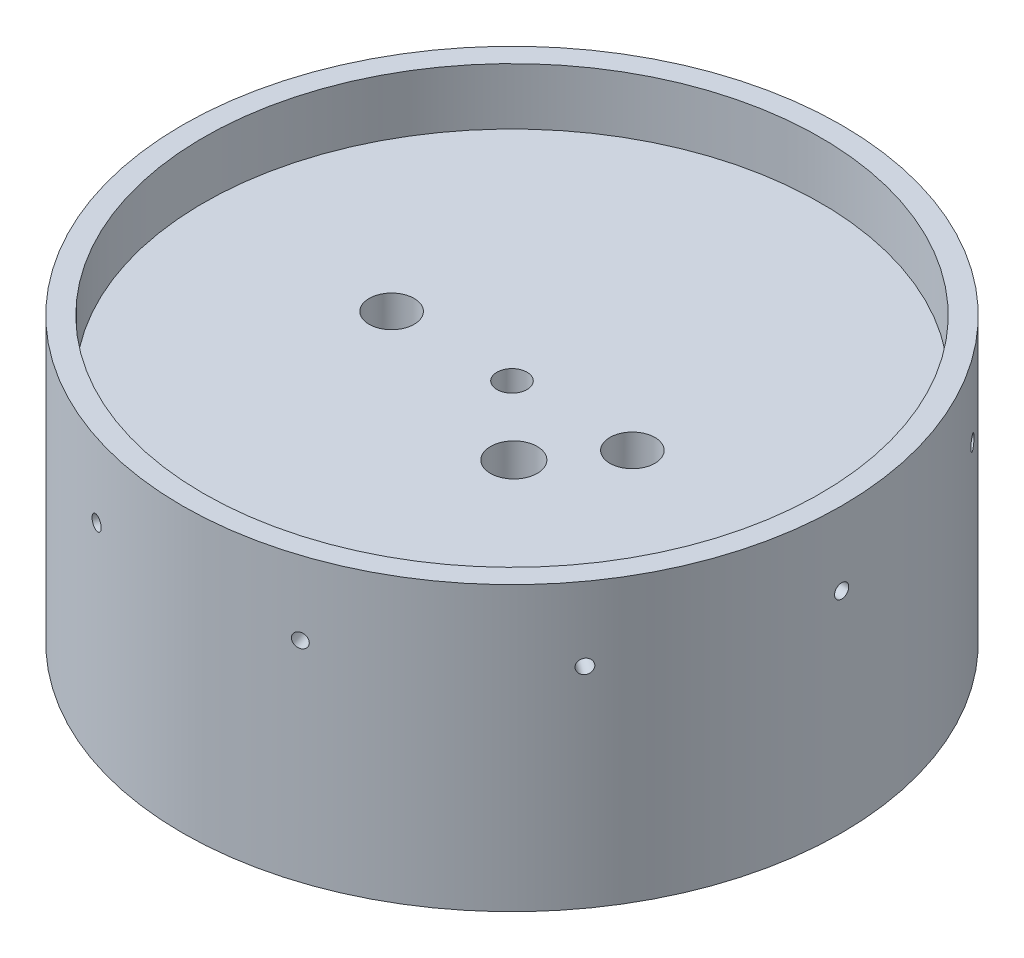
SolidWorks part; units mm, degrees
material "6061 Alloy"
ref_plane "Front Plane" through (0, 0, 0) normal (0, 0, 1) x (1, 0, 0)
ref_plane "Top Plane" through (0, 0, 0) normal (0, 1, 0) x (1, 0, 0)
ref_plane "Right Plane" through (0, 0, 0) normal (1, 0, 0) x (0, 0, -1)
sketch "Sketch1" plane through (0, 0, 0) normal (0, 0, 1) x (1, 0, 0)
  line L0 (0, 0) -> (0, -68.3207) construction
  line L1 (0, -12.7) -> (-69.1515, -12.7)
  line L2 (-69.1515, -12.7) -> (-69.1515, 0)
  line L3 (-69.1515, 0) -> (-73.914, 0)
  line L4 (-73.914, 0) -> (-73.914, -63.5)
  line L5 (-73.914, -63.5) -> (-69.1515, -63.5)
  line L6 (-69.1515, -63.5) -> (-69.1515, -20.32)
  line L7 (-69.1515, -20.32) -> (0, -20.32)
  line L8 (0, -20.32) -> (0, -12.7)
  dimension "D1" = 73.914
  dimension "D2" = 4.7625
  dimension "D3" = 7.62
  dimension "D4" = 12.7
  dimension "D5" = 43.18
revolve "Revolve1" add sketch "Sketch1" angle 360 about L0
sketch "Sketch2" plane through (0, -12.7, 0) normal (0, 1, 0) x (1, 0, 0)
  point P0 (0, 0)
hole_wizard "1/4 Clearance Hole1" positions "Sketch3" profile "Sketch4" hole size "1/4" standard "ANSI Inch" end condition through all
sketch "Sketch3" plane through (0, -12.7, 0) normal (0, 1, 0) x (1, 0, 0)
  point P0 (0, 0)
sketch "Sketch4" plane through (0, -12.7, 0) normal (1, 0, 0) x (0, 0, 1)
  line L0 (0, 0) -> (0, 50.8)
  line L1 (0, 50.8) -> (3.3782, 50.8)
  line L2 (3.3782, 50.8) -> (3.3782, 0)
  line L5 (3.3782, 0) -> (0, 0)
  line L11 (0, -6.35) -> (0, 107.95) construction
  dimension "Thru Hole Dia." = 6.7564
  dimension "Thru Hole Depth" = 50.8
ref_plane "Plane1" through (-73.914, 0, 0) normal (-1, 0, 0) x (0, 0, 1)
sketch "Sketch5" plane through (-73.914, 0, 0) normal (-1, 0, 0) x (0, 0, 1)
  line L0 (0, -63.5) -> (0, -38.1) construction
  line L1 (-73.914, -63.5) -> (73.914, -63.5) construction
  dimension "D1" = 25.4
hole_wizard "1/8 (0.1250) Dowel Hole1" positions "Sketch6" profile "Sketch7" hole size "1/8" standard "ANSI Inch"
sketch "Sketch6" plane through (-73.914, 0, 0) normal (-1, 0, 0) x (0, 0, 1)
  line L0 (0, 0) -> (0, -16.51) construction
  point P0 (0, -16.51)
  dimension "D1" = 16.51
sketch "Sketch7" plane through (-73.914, -16.51, 0) normal (0, 1, 0) x (0, 0, 1)
  line L0 (0, 0) -> (0, 26.3539)
  line L1 (0, 26.3539) -> (1.5875, 25.4)
  line L2 (1.5875, 25.4) -> (1.5875, 0)
  line L5 (1.5875, 0) -> (0, 0)
  line L10 (0, 26.3539) -> (-1.5875, 25.4) construction
  line L11 (0, -6.35) -> (0, 107.95) construction
  dimension "Hole Dia." = 3.175
  dimension "Hole Depth" = 25.4
  dimension "Drill Angle" = 118
pattern_circular "CirPattern2" count 10 over 360 about axis through (0, 0, 0) along (0, 1, 0) of "1/8 (0.1250) Dowel Hole1"
sketch "Sketch8" plane through (0, -12.7, 0) normal (0, 1, 0) x (1, 0, 0)
  line L0 (0, 0) -> (26.9875, 0) construction
  line L1 (0, 0) -> (-26.9875, 0) construction
  point P0 (100.0052, 9.471)
  point P1 (-26.9875, 0)
  point P6 (26.9875, 0)
  dimension "D1" = 26.9875
hole_wizard "3/8 Clearance Hole1" positions "3DSketch1" profile "Sketch11" hole size "3/8" standard "ANSI Inch" end condition through all
sketch3d "3DSketch1"
  point P0 (-26.9875, -12.7, 0)
  point P3 (26.9875, -12.7, 0)
sketch "Sketch11" plane through (-26.9875, -12.7, 0) normal (1, 0, 0) x (0, 0, 1)
  line L0 (0, 0) -> (0, 50.8)
  line L1 (0, 50.8) -> (5.0419, 50.8)
  line L2 (5.0419, 50.8) -> (5.0419, 0)
  line L5 (5.0419, 0) -> (0, 0)
  line L11 (0, -6.35) -> (0, 107.95) construction
  dimension "Thru Hole Dia." = 10.0838
  dimension "Thru Hole Depth" = 50.8
sketch "Sketch12" plane through (0, -20.32, 0) normal (0, -1, 0) x (1, 0, 0)
  circle A0 centre (15.5575, 15.1384) radius 5.2388
  circle A1 centre (26.9875, 0) radius 5.0419 construction
  dimension "D1" = 10.4775
  dimension "D2" = 15.1384
  dimension "D3" = 11.43
extrude "Cut-Extrude1" cut sketch "Sketch12" against normal up to surface (7.62 mm away) up to face at (-26.9875, -12.7, 5.0419)
equation "\"D1@Sketch8\"=2.125/2"
